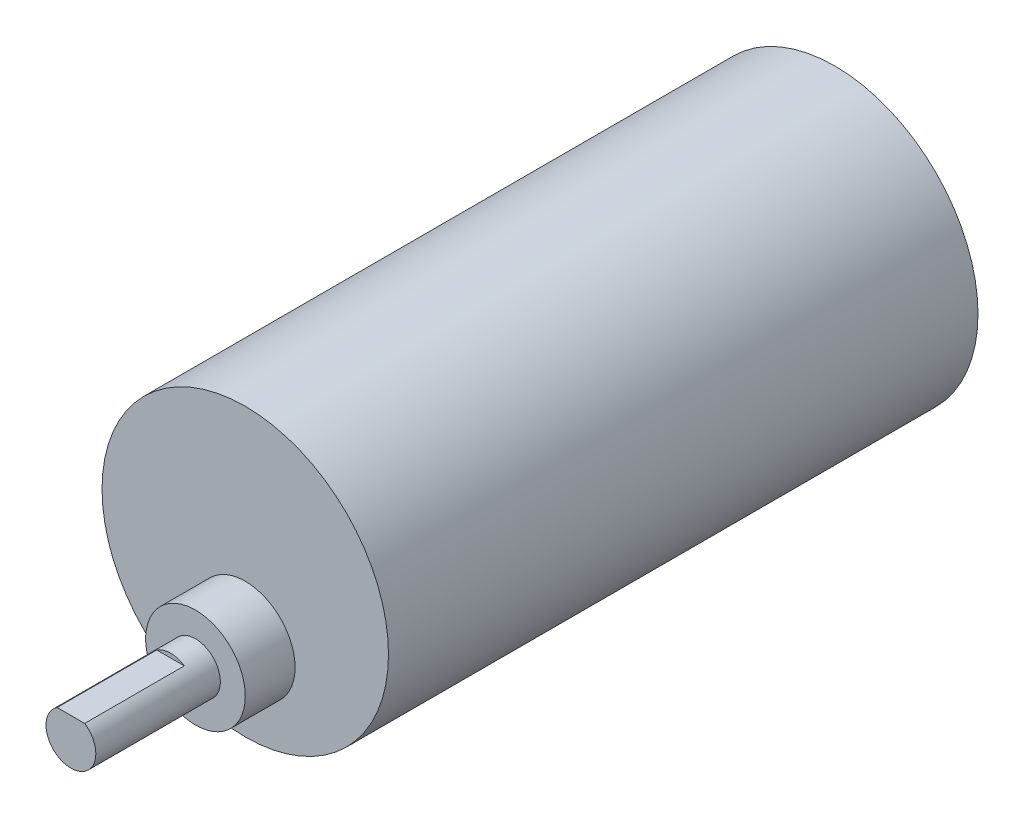
SolidWorks part; units mm, degrees
ref_plane "前视基准面" through (0, 0, 0) normal (0, 0, 1) x (1, 0, 0)
ref_plane "上视基准面" through (0, 0, 0) normal (0, 1, 0) x (1, 0, 0)
ref_plane "右视基准面" through (0, 0, 0) normal (1, 0, 0) x (0, 0, -1)
sketch "草图1" plane through (0, 0, 0) normal (0, 0, 1) x (1, 0, 0)
  circle A0 centre (0, 0) radius 17.25
  dimension "D1" = 34.5
extrude "凸台-拉伸1" add sketch "草图1" along normal blind 71
sketch "草图2" plane through (0, 0, 71) normal (0, 0, 1) x (1, 0, 0)
  line L0 (0, 17.25) -> (0, -17.25) construction
  circle A0 centre (0, 0) radius 17.25 construction
  circle A1 centre (0, -7) radius 6
  point P7 (0, 0)
  dimension "D1" = 7
extrude "凸台-拉伸2" add sketch "草图2" along normal blind 6
sketch "草图3" plane through (0, 0, 77) normal (0, 0, 1) x (1, 0, 0)
  circle A0 centre (0, -7) radius 3
extrude "凸台-拉伸3" add sketch "草图3" along normal blind 15
sketch "草图4" plane through (0, 0, 92) normal (0, 0, 1) x (1, 0, 0)
  line L0 (-3.4073, -4.5) -> (4.6576, -4.5)
  line L1 (-3.4073, -4.5) -> (-3.4073, -3.1728)
  line L2 (-3.4073, -3.1728) -> (3.9699, -3.1728)
  line L3 (3.9699, -3.1728) -> (4.6576, -4.5)
  circle A1 centre (0, -7) radius 3 construction
  dimension "D1" = 2.5
extrude "切除-拉伸1" cut sketch "草图4" against normal blind 12
